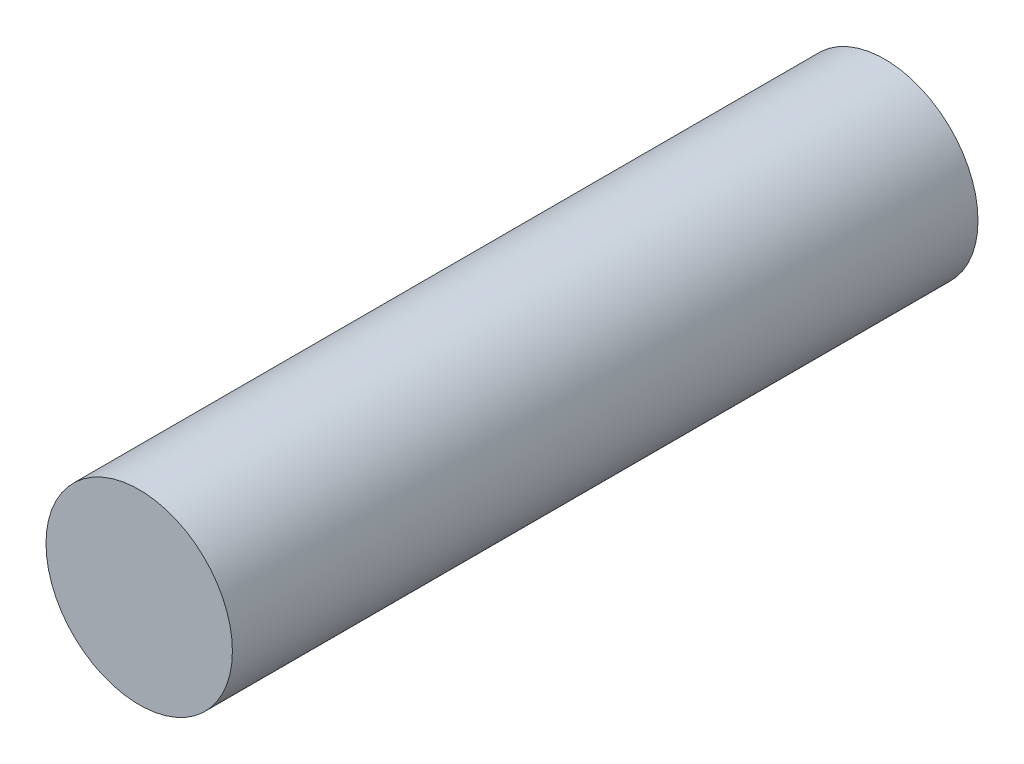
SolidWorks part; units mm, degrees
ref_plane "Front" through (0, 0, 0) normal (0, 0, 1) x (1, 0, 0)
ref_plane "Top" through (0, 0, 0) normal (0, 1, 0) x (-1, 0, 0)
ref_plane "Right" through (0, 0, 0) normal (1, 0, 0) x (0, 0, -1)
sketch "Sketch1" plane through (0, 0, 0) normal (0, 0, 1) x (1, 0, 0)
  circle A0 centre (0, 0) radius 4.7625
  dimension "D1" = 9.525
extrude "Base-Extrude" add sketch "Sketch1" along normal blind 38.1
